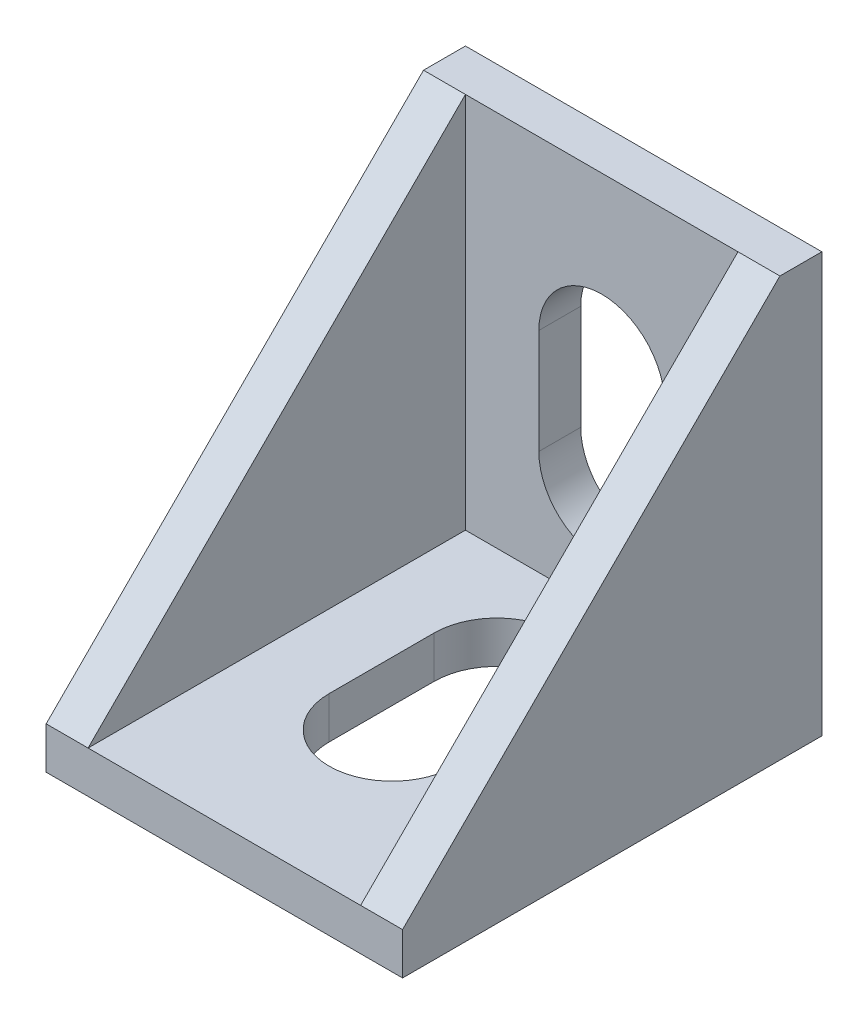
SolidWorks part; units mm, degrees
material "1060 Alloy"
ref_plane "Front Plane" through (0, 0, 0) normal (0, 0, 1) x (1, 0, 0)
ref_plane "Top Plane" through (0, 0, 0) normal (0, 1, 0) x (1, 0, 0)
ref_plane "Right Plane" through (0, 0, 0) normal (1, 0, 0) x (0, 0, -1)
sketch "Sketch1" plane through (0, 0, 0) normal (0, 0, 1) x (1, 0, 0)
  line L1 (-8.5, -10) -> (8.5, -10)
  line L2 (-8.5, -10) -> (-8.5, 10)
  line L3 (-8.5, 10) -> (8.5, 10)
  line L4 (8.5, -10) -> (8.5, 10)
  line L5 (-8.5, -10) -> (8.5, 10) construction
  line L6 (-8.5, 10) -> (8.5, -10) construction
  point P0 (0, 0)
  dimension "D1" = 17
  dimension "D2" = 20
extrude "Boss-Extrude1" add sketch "Sketch1" along normal blind 20
sketch "Sketch2" plane through (0, 10, 0) normal (0, 1, 0) x (1, 0, 0)
  line L0 (8.5, -20) -> (-8.5, -20) construction
  line L1 (-6.5, -20) -> (6.5, -20)
  line L2 (-6.5, -20) -> (-6.5, -2)
  line L3 (-6.5, -2) -> (6.5, -2)
  line L4 (6.5, -20) -> (6.5, -2)
  line L5 (-8.5, -20) -> (-8.5, 0) construction
  line L6 (8.5, -20) -> (8.5, 0) construction
  line L7 (8.5, 0) -> (-8.5, 0) construction
  dimension "D1" = 2
  dimension "D2" = 2
  dimension "D3" = 2
extrude "Cut-Extrude1" cut sketch "Sketch2" against normal blind 18
sketch "Sketch3" plane through (8.5, 0, 0) normal (1, 0, 0) x (0, 0, -1)
  line L0 (-2, 10) -> (-20, -8)
  line L1 (-20, 10) -> (0, 10) construction
  line L2 (-20, -10) -> (-20, 10) construction
  line L3 (-20, -8) -> (-20, 10)
  line L4 (-20, 10) -> (-2, 10)
  dimension "D1" = 18
  dimension "D2" = 18
extrude "Cut-Extrude2" cut sketch "Sketch3" against normal through all and the other way through all
sketch "Sketch4" plane through (0, -8, 0) normal (0, 1, 0) x (1, 0, 0)
  line L0 (0, -12) -> (0, -7) construction
  line L1 (-3, -12) -> (-3, -7)
  line L2 (3, -12) -> (3, -7)
  line L3 (0, -7) -> (0, -2) construction
  line L4 (6.5, -2) -> (-6.5, -2) construction
  arc A0 (-3, -12) -> (3, -12) centre (0, -12) ccw
  arc A1 (3, -7) -> (-3, -7) centre (0, -7) ccw
  point P3 (0, -9.5)
  dimension "D1" = 3
  dimension "D2" = 5
  dimension "D3" = 5
extrude "Cut-Extrude3" cut sketch "Sketch4" against normal up to next
sketch "Sketch5" plane through (0, 0, 2) normal (0, 0, 1) x (1, 0, 0)
  line L0 (0, -3) -> (0, 2) construction
  line L1 (-3, -3) -> (-3, 2)
  line L2 (3, -3) -> (3, 2)
  line L3 (6.5, -8) -> (-6.5, -8) construction
  arc A0 (-3, -3) -> (3, -3) centre (0, -3) ccw
  arc A1 (3, 2) -> (-3, 2) centre (0, 2) ccw
  point P3 (0, -0.5)
  dimension "D1" = 3
  dimension "D2" = 5
  dimension "D3" = 5
extrude "Cut-Extrude4" cut sketch "Sketch5" against normal up to next
sketch "Sketch6" plane through (0, -10, 0) normal (0, -1, 0) x (1, 0, 0)
  line L0 (-1, 18) -> (1, 18) construction
  line L1 (-1, 19) -> (1, 19)
  line L2 (-1, 17) -> (1, 17)
  line L3 (0, 18) -> (0, 20) construction
  line L4 (-8.5, 20) -> (8.5, 20) construction
  line L5 (-1, 2) -> (1, 2) construction
  line L6 (-1, 3) -> (1, 3)
  line L7 (-1, 1) -> (1, 1)
  line L8 (0, 18) -> (0, 2) construction
  line L9 (-8.5, 0) -> (8.5, 0) construction
  arc A0 (-1, 19) -> (-1, 17) centre (-1, 18) ccw
  arc A1 (1, 17) -> (1, 19) centre (1, 18) ccw
  arc A2 (-1, 3) -> (-1, 1) centre (-1, 2) ccw
  arc A3 (1, 1) -> (1, 3) centre (1, 2) ccw
  point P2 (0, 18)
  point P13 (0, 2)
  dimension "D1" = 1
  dimension "D2" = 2
  dimension "D3" = 2
  dimension "D4" = 2
extrude "Boss-Extrude2" add sketch "Sketch6" along normal blind 1
sketch "Sketch7" plane through (0, 0, 0) normal (0, 0, -1) x (-1, 0, 0)
  line L0 (1, -8) -> (-1, -8) construction
  line L1 (1, -9) -> (-1, -9)
  line L2 (1, -7) -> (-1, -7)
  line L3 (1, 8) -> (-1, 8) construction
  line L4 (1, 7) -> (-1, 7)
  line L5 (1, 9) -> (-1, 9)
  line L6 (0, -8) -> (0, -10) construction
  line L7 (8.5, -10) -> (-8.5, -10) construction
  line L8 (0, -8) -> (0, 8) construction
  line L9 (-8.5, 10) -> (8.5, 10) construction
  arc A0 (1, -9) -> (1, -7) centre (1, -8) ccw
  arc A1 (-1, -7) -> (-1, -9) centre (-1, -8) ccw
  arc A2 (1, 7) -> (1, 9) centre (1, 8) ccw
  arc A3 (-1, 9) -> (-1, 7) centre (-1, 8) ccw
  point P2 (0, -8)
  point P7 (0, 8)
  dimension "D3" = 1
  dimension "D4" = 2
  dimension "D1" = 2
  dimension "D2" = 2
extrude "Boss-Extrude3" add sketch "Sketch7" along normal blind 1
